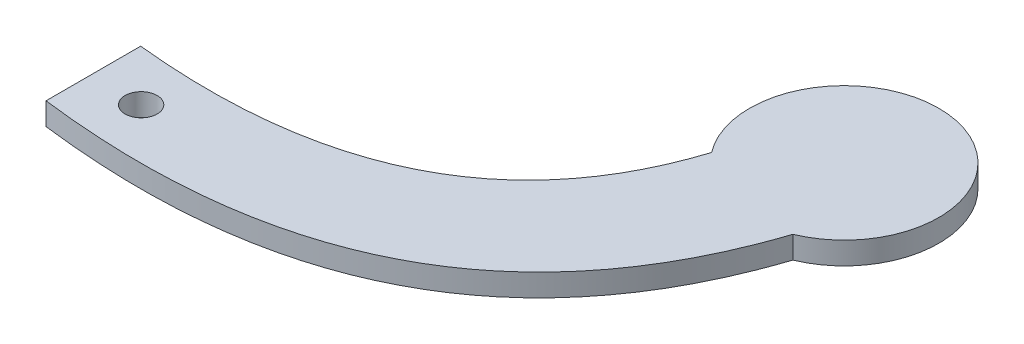
SolidWorks part; units mm, degrees
ref_plane "Front Plane" through (0, 0, 0) normal (0, 0, 1) x (1, 0, 0)
ref_plane "Top Plane" through (0, 0, 0) normal (0, 1, 0) x (1, 0, 0)
ref_plane "Right Plane" through (0, 0, 0) normal (1, 0, 0) x (0, 0, -1)
sketch "Sketch2" plane through (0, 0, 0) normal (0, 1, 0) x (1, 0, 0)
  line L0 (-37.697, 4.281) -> (-37.697, -8.419)
  line L1 (14.2475, 35.0628) -> (29.3687, 31.1237)
  spline S0 degree 2 poles (-37.697, 4.281) (6.488, -0.3233) (14.2475, 35.0628) knots 0 0 0 1 1 1
  spline S1 degree 2 poles (-37.697, -8.419) (17.3809, -15.2774) (29.3687, 31.1237) knots 0 0 0 1 1 1
  dimension "D1" = 12.7
extrude "Boss-Extrude1" add sketch "Sketch2" along normal blind 3
sketch "Sketch3" plane through (0, 0, 0) normal (0, 1, 0) x (1, 0, 0)
  line L0 (21.8081, 33.0933) -> (23.0634, 37.912) construction
  line L1 (29.3687, 31.1237) -> (14.2475, 35.0628) construction
  circle A0 centre (23.0634, 37.912) radius 12.7
  dimension "D1" = 25.4
extrude "Boss-Extrude2" add sketch "Sketch3" along normal blind 3
hole_wizard "#8 Clearance Hole1" positions "Sketch5" profile "Sketch4" hole size "#8" standard "ANSI Inch" end condition through all
sketch "Sketch5" plane through (0, 3, 0) normal (0, 1, 0) x (1, 0, 0)
  point P0 (-30.8552, -2.4961)
sketch "Sketch4" plane through (-30.8552, 3, 2.4961) normal (1, 0, 0) x (0, 0, 1)
  line L0 (0, 0) -> (0, 3)
  line L1 (0, 3) -> (2.1526, 3)
  line L2 (2.1526, 3) -> (2.1526, 0)
  line L5 (2.1526, 0) -> (0, 0)
  line L11 (0, -6.35) -> (0, 107.95) construction
  dimension "Thru Hole Dia." = 4.3053
  dimension "Thru Hole Depth" = 3
